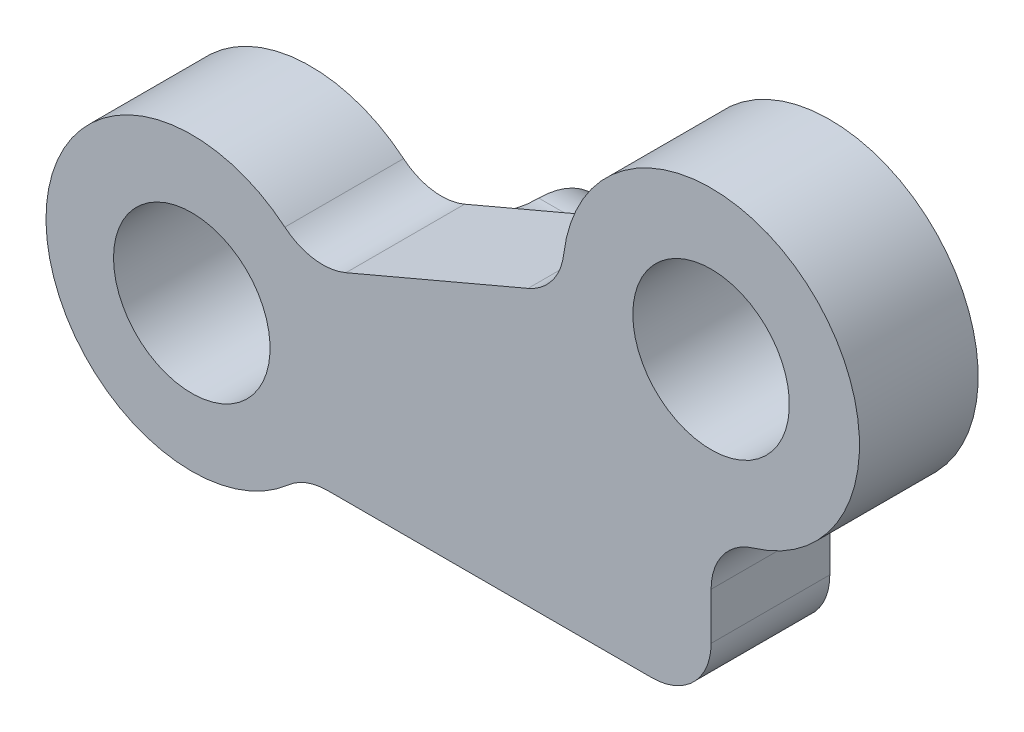
SolidWorks part; units mm, degrees
material "PLA"
ref_plane "Front Plane" through (0, 0, 0) normal (0, 0, 1) x (1, 0, 0)
ref_plane "Top Plane" through (0, 0, 0) normal (0, 1, 0) x (1, 0, 0)
ref_plane "Right Plane" through (0, 0, 0) normal (1, 0, 0) x (0, 0, -1)
ref_plane "Plane3" through (0, 0, 0) normal (0, 0, -1) x (-1, 0, 0)
sketch "Sketch17" plane through (0, 0, 0) normal (0, 0, -1) x (-1, 0, 0)
  line L0 (-43.2731, 29.4209) -> (-51.8645, 33.076)
  line L1 (-56.8391, 28.5799) -> (-56.8391, 23.2923)
  line L2 (-56.8391, 23.2923) -> (-43.0826, 23.2923)
  arc A0 (-43.0826, 23.2923) -> (-43.2731, 29.4209) centre (-39.3406, 26.4759) ccw
  arc A1 (-51.8645, 33.076) -> (-56.8391, 28.5799) centre (-56.8391, 33.5799) ccw
extrude "Boss-Extrude3" add sketch "Sketch17" against normal blind 4
hole_wizard "Hole3" positions "Sketch19" profile "Sketch18" legacy
sketch "Sketch19" plane through (0, 0, 0) normal (0, 0, -1) x (-1, 0, 0)
  point P0 (-39.3406, 26.4759)
  point P1 (-56.8391, 33.5799)
sketch "Sketch18" plane through (39.3406, 26.4759, 0) normal (1, 0, 0) x (0, 1, 0)
  line L0 (0, 0) -> (0, 4)
  line L1 (0, 4) -> (2.6375, 4)
  line L2 (2.6375, 4) -> (2.6375, 0)
  line L3 (2.6375, 0) -> (0, 0)
  line L4 (0, 110) -> (0, -10) construction
  dimension "Diameter" = 5.275
  dimension "Depth" = 4
fillet "Fillet3" radius 2 5 edges at (51.8645, 33.076, 2) (43.0826, 23.2923, 2) (43.2731, 29.4209, 2) (56.8391, 23.2923, 2) (56.8391, 28.5799, 2)
ref_plane "Plane4" through (45, 0, 0) normal (1, 0, 0) x (0, 0, -1)
ref_plane "Plane5" through (47, 0, 0) normal (1, 0, 0) x (0, 0, -1)
sketch "Sketch25" plane through (47, 0, 0) normal (1, 0, 0) x (0, 0, -1)
  line L0 (0, 23.2923) -> (0, 30.1441)
  line L1 (0, 28.7883) -> (0, 38.5799) construction
  circle A0 centre (2.034, 26.8496) radius 1.5065
  arc A1 (2.034, 24.3496) -> (2.034, 29.3496) centre (2.034, 26.8496) ccw
  spline S0 degree 2 poles (2.034, 29.3496) (0.8443, 29.3488) (0, 30.1441) knots 0 0 0 1 1 1
  spline S1 degree 2 poles (2.034, 24.3496) (0.7258, 24.3594) (0, 23.2923) knots 0 0 0 1 1 1
extrude "Boss-Extrude4" add sketch "Sketch25" against normal up to surface (2 mm away) up to plane "Plane4"
